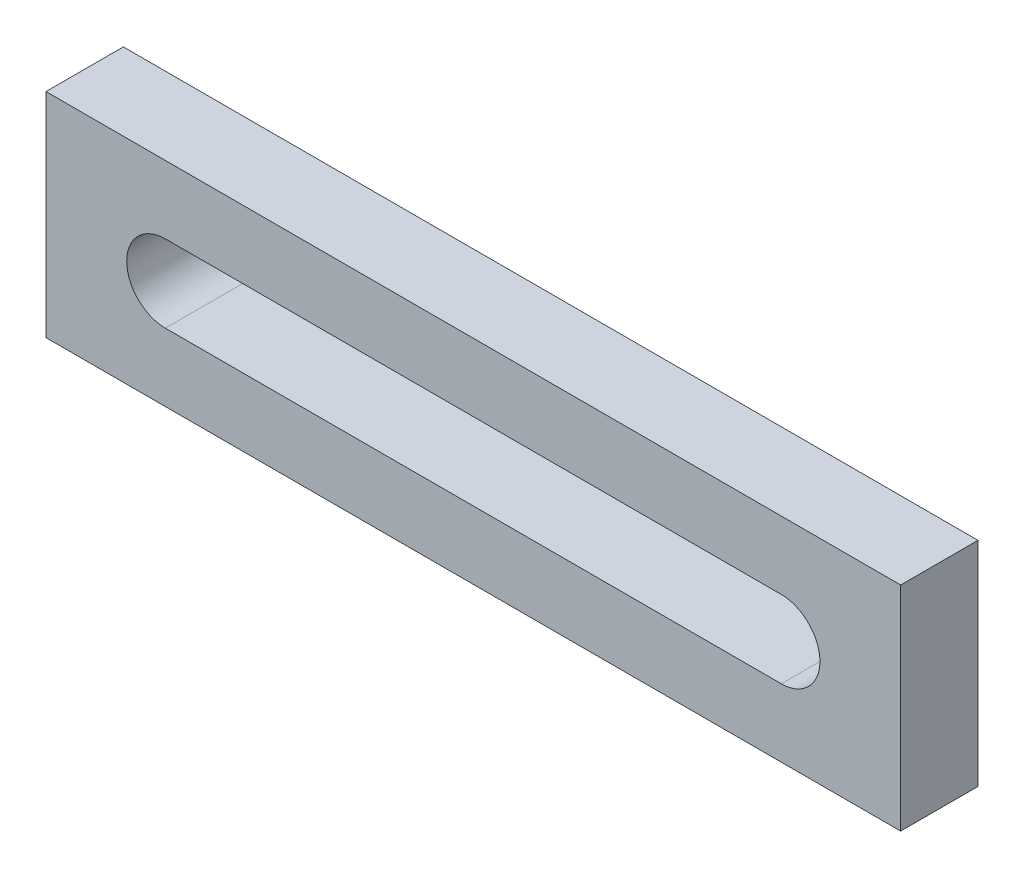
SolidWorks part; units mm, degrees
ref_plane "Front" through (0, 0, 0) normal (0, 0, 1) x (1, 0, 0)
ref_plane "Top" through (0, 0, 0) normal (0, 1, 0) x (1, 0, 0)
ref_plane "Right" through (0, 0, 0) normal (1, 0, 0) x (0, 0, -1)
sketch "Sketch1" plane through (0, 0, 0) normal (0, 0, 1) x (1, 0, 0)
  line L0 (0, 13.7805) -> (110.5101, 13.7805) construction
  line L1 (0, 0) -> (110.5101, 0)
  line L2 (0, 0) -> (0, 27.561)
  line L3 (0, 27.561) -> (110.5101, 27.561)
  line L4 (110.5101, 0) -> (110.5101, 27.561)
  line L5 (15.4358, 13.7805) -> (95.0744, 13.7805) construction
  line L6 (15.4358, 18.7805) -> (95.0744, 18.7805)
  line L7 (15.4358, 8.7805) -> (95.0744, 8.7805)
  arc A0 (15.4358, 18.7805) -> (15.4358, 8.7805) centre (15.4358, 13.7805) ccw
  arc A1 (95.0744, 8.7805) -> (95.0744, 18.7805) centre (95.0744, 13.7805) ccw
  circle A3 centre (15.4358, 13.7805) radius 5 construction
  point P9 (55.2551, 13.7805)
extrude "Boss-Extrude1" add sketch "Sketch1" along normal blind 10
